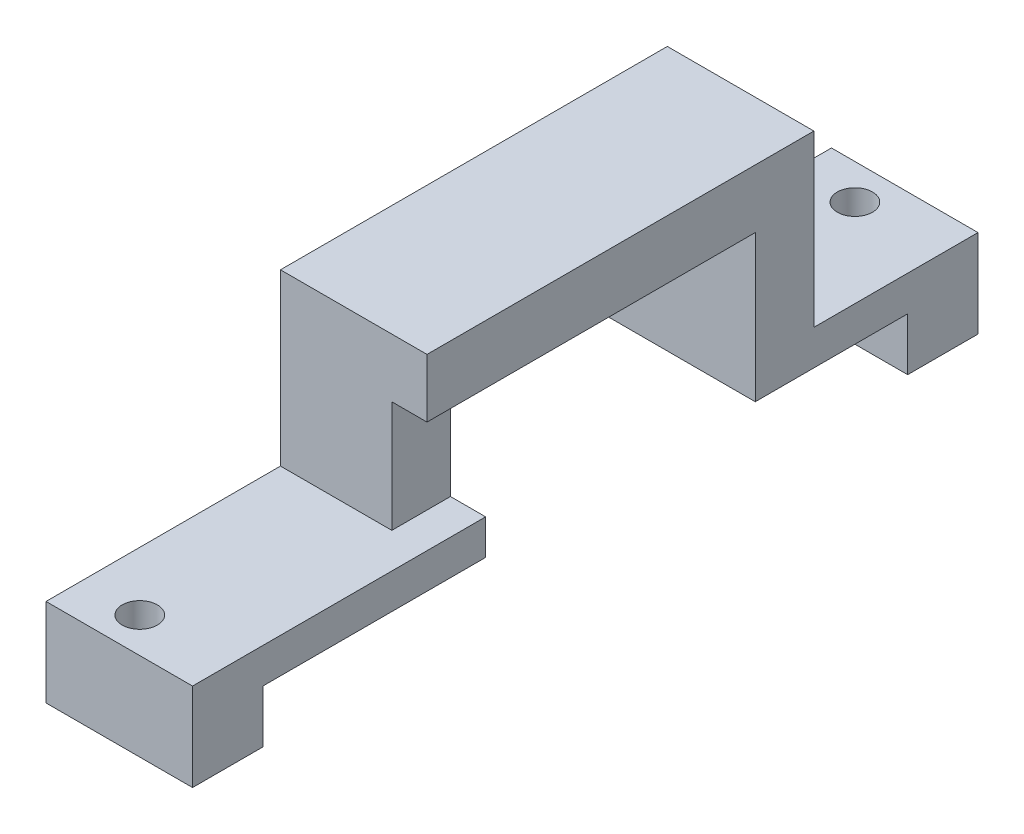
SolidWorks part; units mm, degrees
ref_plane "Front Plane" through (0, 0, 0) normal (0, 0, 1) x (1, 0, 0)
ref_plane "Top Plane" through (0, 0, 0) normal (0, 1, 0) x (1, 0, 0)
ref_plane "Right Plane" through (0, 0, 0) normal (1, 0, 0) x (0, 0, -1)
sketch "Sketch2" plane through (0, 0, 0) normal (1, 0, 0) x (0, 0, -1)
  line L0 (6, 0) -> (25, 0)
  line L1 (0, 3) -> (20, 3)
  line L2 (25, 0) -> (25, 12.5)
  line L3 (25, 12.5) -> (48, 12.5)
  line L4 (48, 12.5) -> (48, 0)
  line L5 (53, 3) -> (67, 3)
  line L6 (0, 3) -> (67, 3) construction
  line L7 (20, 3) -> (20, 17.5)
  line L8 (20, 17.5) -> (53, 17.5)
  line L9 (53, 17.5) -> (53, 3)
  line L10 (0, 3) -> (0, 0)
  line L11 (67, 3) -> (67, 0)
  line L12 (20, 0) -> (20, 17.5) construction
  line L13 (53, 17.5) -> (53, 0) construction
  line L14 (48, 0) -> (61, 0)
  line L15 (0, 0) -> (67, 0) construction
  line L16 (0, 0) -> (0, -4.5)
  line L17 (0, -4.5) -> (6, -4.5)
  line L18 (6, -4.5) -> (6, 0)
  line L19 (61, -4.5) -> (67, -4.5)
  line L20 (67, -4.5) -> (67, 0)
  line L21 (61, -4.5) -> (61, 0)
  dimension "D1" = 67
  dimension "D3" = 23
  dimension "D4" = 19
  dimension "D5" = 12.5
  dimension "D7" = 4.5
  dimension "D8" = 6
  dimension "D9" = 6
  dimension "D2" = 3
  dimension "D6" = 5
extrude "Boss-Extrude1" add sketch "Sketch2" along normal blind 12.5
sketch "Sketch3" plane through (0, 3, 0) normal (0, 1, 0) x (1, 0, 0)
  line L0 (12.5, 0) -> (0, 0) construction
  line L1 (12.5, 20) -> (12.5, 0) construction
  line L2 (12.5, 0) -> (12.5, 67) construction
  line L3 (12.5, 33.5) -> (7.5, 33.5) construction
  circle A0 centre (7.5, 3) radius 1.5
  circle A1 centre (7.5, 64) radius 1.5
  dimension "D1" = 3
  dimension "D2" = 3
  dimension "D3" = 5
extrude "Cut-Extrude1" cut sketch "Sketch3" against normal blind 12.5
sketch "Sketch4" plane through (0, 0, -20) normal (0, 0, 1) x (1, 0, 0)
  line L7 (12.5, 12.5) -> (0, 12.5) construction
  line L8 (0, 3) -> (3, 3)
  line L9 (0, 3) -> (0, 12.5)
  line L10 (0, 12.5) -> (3, 12.5)
  line L11 (3, 3) -> (3, 12.5)
  dimension "D1" = 3
extrude "Cut-Extrude2" cut sketch "Sketch4" against normal blind 5
mirror "Mirror1" about plane through (0, 0, 0) normal (1, 0, 0) of bodies 103
sketch "Sketch5" plane through (0, 0, 0) normal (1, 0, 0) x (0, 0, -1)
  line L1 (-2.161, 18.192) -> (78.594, 18.192)
  line L2 (-2.161, 18.192) -> (-2.161, -15.8784)
  line L3 (-2.161, -15.8784) -> (78.594, -15.8784)
  line L4 (78.594, 18.192) -> (78.594, -15.8784)
extrude "Cut-Extrude3" cut sketch "Sketch5" along normal blind 29.5
sketch "Sketch6" plane through (-12.5, 0, 0) normal (-1, 0, 0) x (0, 0, 1)
  line L0 (-25, 0) -> (-25, 12.5) construction
  line L1 (-48, 12.5) -> (-48, 0) construction
  line L2 (-25, 0) -> (-25, 12.5) construction
  line L3 (-48, 12.5) -> (-48, 0) construction
  line L4 (-48, 6.25) -> (-25, 6.25) construction
  line L5 (-36.5, 8.1464) -> (-36.5, 1.5418) construction
  circle A0 centre (-50.35, 6.25) radius 1
  circle A1 centre (-22.65, 6.25) radius 1
  point P8 (-36.5, 6.25)
  dimension "D2" = 2
  dimension "D1" = 13.85
extrude "Cut-Extrude5" cut sketch "Sketch6" against normal blind 3
